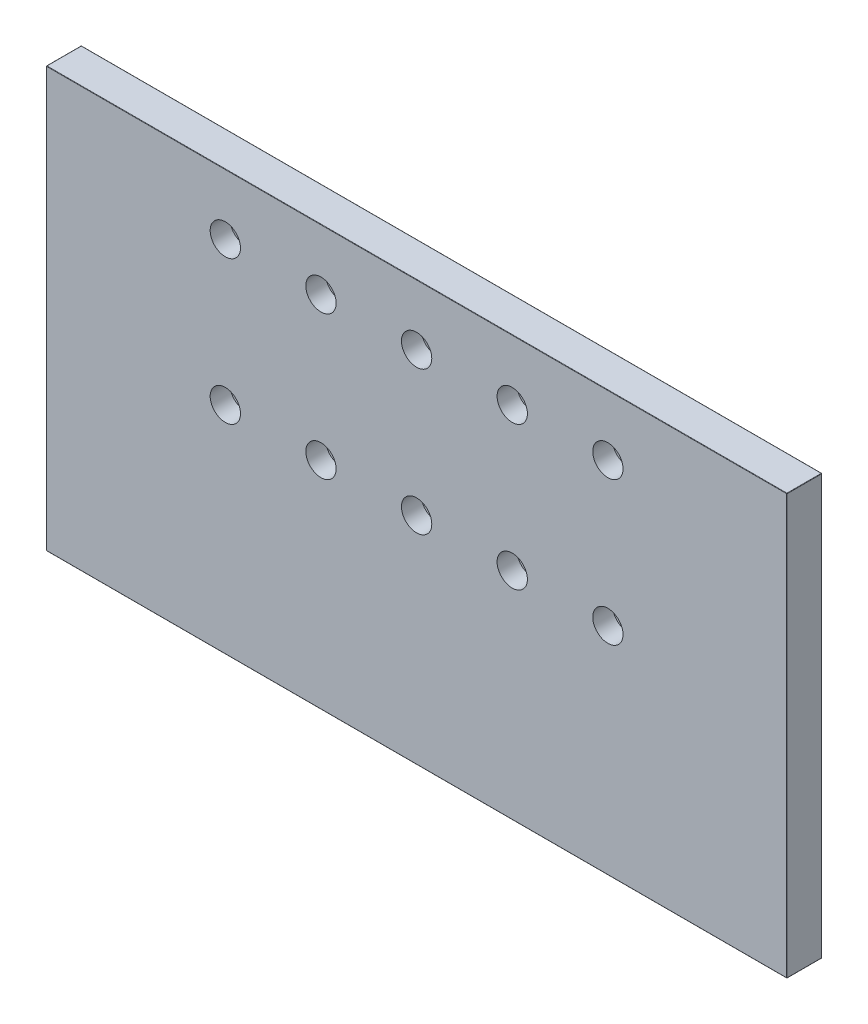
SolidWorks part; units mm, degrees
ref_plane "Front Plane" through (0, 0, 0) normal (0, 0, 1) x (1, 0, 0)
ref_plane "Top Plane" through (0, 0, 0) normal (0, 1, 0) x (1, 0, 0)
ref_plane "Right Plane" through (0, 0, 0) normal (1, 0, 0) x (0, 0, -1)
sketch "Sketch2" plane through (0, 0, 0) normal (0, 0, 1) x (1, 0, 0)
  line L1 (0, 0) -> (635, 0)
  line L2 (0, 0) -> (0, 360)
  line L3 (0, 360) -> (635, 360)
  line L4 (635, 0) -> (635, 360)
  dimension "D1" = 360
  dimension "D2" = 635
extrude "Boss-Extrude1" add sketch "Sketch2" along normal blind 30
sketch "Sketch3" plane through (0, 0, 30) normal (0, 0, 1) x (1, 0, 0)
  circle A0 centre (153.5, 308) radius 13
  dimension "D1" = 26
  dimension "D2" = 308
  dimension "D3" = 153.5
extrude "Cut-Extrude2" cut sketch "Sketch3" against normal blind 17
sketch "Sketch4" plane through (0, 0, 13) normal (0, 0, 1) x (1, 0, 0)
  circle A0 centre (153.5, 308) radius 8
  dimension "D1" = 16
extrude "Cut-Extrude3" cut sketch "Sketch4" against normal through all
pattern_linear "LPattern1" count 5 spacing 82 along (1, 0, 0) count 2 spacing 123 along (0, -1, 0) of "Cut-Extrude3", "Cut-Extrude2"
fillet "Fillet1" radius 0.3 11 edges at (0, 0, 15) (317.5, 0, 30) (317.5, 0, 0) (0, 180, 0) (0, 360, 15) (635, 360, 15) (635, 0, 15) (635, 180, 30) (635, 180, 0) (317.5, 360, 0) (317.5, 360, 30)
sketch "Sketch7" plane through (0, 0, 0) normal (0, -1, 0) x (1, 0, 0)
  circle A0 centre (10, 20) radius 5
  point P5 (-2.9637, -0.0221)
  dimension "D1" = 10
  dimension "D2" = 20
  dimension "D3" = 10
extrude "Cut-Extrude4" cut sketch "Sketch7" against normal blind 18
pattern_linear "LPattern2" count 10 spacing 68.3 along (1, 0, 0) of "Cut-Extrude4"
sketch3d "3DSketch1"
  point P0 (570.5848, 111.975, 30)
